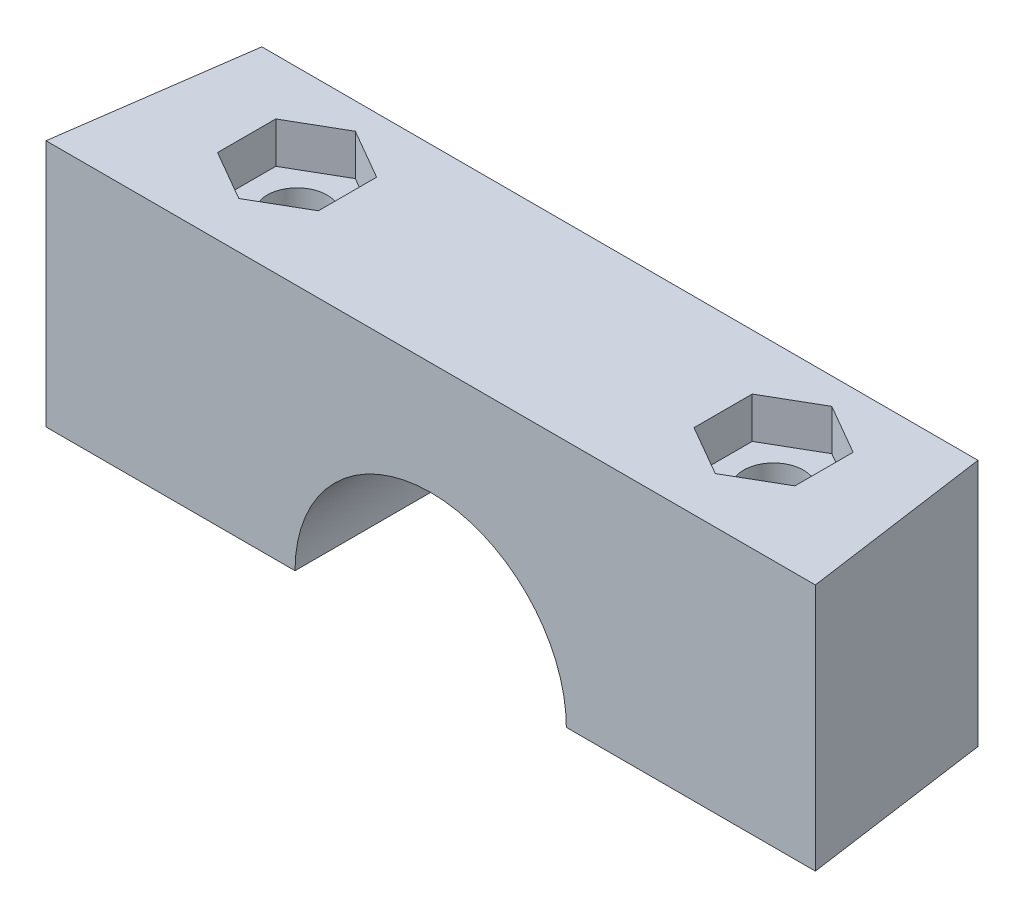
SolidWorks part; units mm, degrees
ref_plane "Front Plane" through (0, 0, 0) normal (0, 0, 1) x (1, 0, 0)
ref_plane "Top Plane" through (0, 0, 0) normal (0, 1, 0) x (1, 0, 0)
ref_plane "Right Plane" through (0, 0, 0) normal (1, 0, 0) x (0, 0, -1)
sketch "Sketch6" plane through (0, 0, 0) normal (0, 1, 0) x (1, 0, 0)
  line L0 (-16.8369, 5.7834) -> (13.1631, 5.7834)
  line L1 (13.1631, 5.7834) -> (20.6631, -47.5819)
  line L2 (20.6631, -47.5819) -> (-24.3369, -47.5819)
  line L3 (-24.3369, -47.5819) -> (-16.8369, 5.7834)
  circle A0 centre (13.1631, -5.2166) radius 1.78
  circle A1 centre (-16.8369, -5.2166) radius 1.78
  circle A2 centre (-26.4869, -43.0491) radius 1.78
  circle A3 centre (22.8131, -43.0491) radius 1.78
  dimension "D3" = 98
  dimension "D4" = 3.56
  dimension "D5" = 3.56
  dimension "D2" = 45
  dimension "D6" = 30
  dimension "D7" = 11
  dimension "D8" = 11
  dimension "D9" = 98
  dimension "D10" = 82
  dimension "D11" = 82
  dimension "D12" = 30
extrude "Boss-Extrude3" add sketch "Sketch6" along normal blind 14.5 contours L3 L0 L1 L2
sketch "Sketch8" plane through (0, 0, 47.5819) normal (0, 0, 1) x (1, 0, 0)
  line L0 (20.6631, 0) -> (-24.3369, 0) construction
  circle A0 centre (-1.8369, 0) radius 7.935
  dimension "D1" = 15.87
extrude "Cut-Extrude3" cut sketch "Sketch8" against normal blind 88
sketch "Sketch18" plane through (0, 14.5, 0) normal (0, 1, 0) x (1, 0, 0)
  line L0 (20.6631, -47.5819) -> (-24.3369, -47.5819) construction
  line L1 (-24.3369, -47.5819) -> (-16.8369, 5.7834) construction
  line L2 (13.1631, 5.7834) -> (20.6631, -47.5819) construction
  line L10 (-15.7718, -44.8683) -> (-12.8218, -43.1651)
  line L11 (-12.8218, -43.1651) -> (-12.8218, -39.7587)
  line L12 (-12.8218, -39.7587) -> (-15.7718, -38.0556)
  line L13 (-15.7718, -38.0556) -> (-18.7218, -39.7587)
  line L14 (-18.7218, -39.7587) -> (-18.7218, -43.1651)
  line L15 (-18.7218, -43.1651) -> (-15.7718, -44.8683)
  line L16 (12.098, -44.8683) -> (15.048, -43.1651)
  line L17 (15.048, -43.1651) -> (15.048, -39.7587)
  line L18 (15.048, -39.7587) -> (12.098, -38.0556)
  line L19 (12.098, -38.0556) -> (9.148, -39.7587)
  line L20 (9.148, -39.7587) -> (9.148, -43.1651)
  line L21 (9.148, -43.1651) -> (12.098, -44.8683)
  line L22 (11.3893, -26.016) -> (14.3893, -24.284)
  line L23 (14.3893, -24.284) -> (14.3893, -20.8199)
  line L24 (14.3893, -20.8199) -> (11.3893, -19.0878)
  line L25 (11.3893, -19.0878) -> (8.3893, -20.8199)
  line L26 (8.3893, -20.8199) -> (8.3893, -24.284)
  line L27 (8.3893, -24.284) -> (11.3893, -26.016)
  line L28 (-15.0632, -26.016) -> (-12.0632, -24.284)
  line L29 (-12.0632, -24.284) -> (-12.0632, -20.8199)
  line L30 (-12.0632, -20.8199) -> (-15.0632, -19.0878)
  line L31 (-15.0632, -19.0878) -> (-18.0632, -20.8199)
  line L32 (-18.0632, -20.8199) -> (-18.0632, -24.284)
  line L33 (-18.0632, -24.284) -> (-15.0632, -26.016)
  circle A0 centre (-15.0632, -22.5519) radius 3 construction
  circle A1 centre (-15.7718, -41.4619) radius 2.95 construction
  circle A2 centre (12.098, -41.4619) radius 2.95 construction
  circle A3 centre (11.3893, -22.5519) radius 3 construction
  point P0 (-15.7718, -41.4619)
  point P1 (-15.0632, -22.5519)
  point P2 (12.098, -41.4619)
  point P3 (11.3893, -22.5519)
  dimension "D1" = 6.12
  dimension "D2" = 7.63
  dimension "D3" = 25.03
  dimension "D4" = 5.7
  dimension "D5" = 6.12
  dimension "D6" = 7.63
  dimension "D7" = 25.03
  dimension "D8" = 5.7
  dimension "D9" = 6
  dimension "D10" = 5.9
  dimension "D11" = 5.9
  dimension "D12" = 6
sketch "Sketch19" plane through (0, 0, 0) normal (0, -1, 0) x (1, 0, 0)
  line L1 (-20.0152, 40.7177) -> (-17.249, 37.4149)
  line L2 (-17.249, 37.4149) -> (-13.0056, 38.1592)
  line L3 (-13.0056, 38.1592) -> (-11.5284, 42.2062)
  line L4 (-11.5284, 42.2062) -> (-14.2947, 45.5089)
  line L5 (-14.2947, 45.5089) -> (-18.5381, 44.7647)
  line L6 (-18.5381, 44.7647) -> (-20.0152, 40.7177)
  line L7 (-16.9187, 22.0232) -> (-15.5331, 20.6806)
  line L8 (-15.5331, 20.6806) -> (-13.6775, 21.2093)
  line L9 (-13.6775, 21.2093) -> (-13.2076, 23.0806)
  line L10 (-13.2076, 23.0806) -> (-14.5932, 24.4232)
  line L11 (-14.5932, 24.4232) -> (-16.4488, 23.8945)
  line L12 (-16.4488, 23.8945) -> (-16.9187, 22.0232)
  line L13 (16.8606, 20.993) -> (15.475, 26.5108)
  line L14 (15.475, 26.5108) -> (10.0037, 28.0696)
  line L15 (10.0037, 28.0696) -> (5.918, 24.1108)
  line L16 (5.918, 24.1108) -> (7.3037, 18.5931)
  line L17 (7.3037, 18.5931) -> (12.775, 17.0342)
  line L18 (12.775, 17.0342) -> (16.8606, 20.993)
  line L19 (20.0445, 40.0682) -> (17.2783, 47.6469)
  line L20 (17.2783, 47.6469) -> (9.3318, 49.0407)
  line L21 (9.3318, 49.0407) -> (4.1515, 42.8557)
  line L22 (4.1515, 42.8557) -> (6.9177, 35.2769)
  line L23 (6.9177, 35.2769) -> (14.8642, 33.8832)
  line L24 (14.8642, 33.8832) -> (20.0445, 40.0682)
  circle A0 centre (-15.7718, 41.4619) radius 3.731 construction
  circle A1 centre (-15.0632, 22.5519) radius 1.6709 construction
  circle A2 centre (11.3893, 22.5519) radius 4.9269 construction
  circle A3 centre (12.098, 41.4619) radius 6.9869 construction
  point P0 (-15.7718, 41.4619)
  point P1 (-15.0632, 22.5519)
  point P3 (11.3893, 22.5519)
  point P5 (12.098, 41.4619)
extrude "Cut-Extrude9" cut sketch "Sketch18" against normal blind 2.4
hole_wizard "#39 (0.13779528) Diameter Hole1" positions "3DSketch1" profile "Sketch21" hole size "#39" standard "ANSI Inch" end condition through all
sketch3d "3DSketch1"
  point P0 (-15.0632, 14.5, 22.5519)
  point P3 (11.3893, 14.5, 22.5519)
  point P6 (-15.7718, 14.5, 41.4619)
  point P9 (12.098, 14.5, 41.4619)
sketch "Sketch21" plane through (-15.0632, 14.5, 22.5519) normal (1, 0, 0) x (0, 0, 1)
  line L0 (0, 0) -> (0, 14.5)
  line L1 (0, 14.5) -> (1.75, 14.5)
  line L2 (1.75, 14.5) -> (1.75, 0)
  line L5 (1.75, 0) -> (0, 0)
  line L11 (0, -6.35) -> (0, 107.95) construction
  dimension "Thru Hole Dia." = 3.5
  dimension "Thru Hole Depth" = 14.5
sketch "Sketch22" plane through (0, 14.5, 0) normal (0, 1, 0) x (1, 0, 0)
  line L0 (-22.7813, -36.5132) -> (19.1075, -36.5132)
  line L1 (-24.3369, -47.5819) -> (-16.8369, 5.7834) construction
  line L2 (13.1631, 5.7834) -> (20.6631, -47.5819) construction
  line L3 (19.1075, -36.5132) -> (13.1631, 5.7834)
  line L4 (13.1631, 5.7834) -> (-16.8369, 5.7834)
  line L5 (-16.8369, 5.7834) -> (-22.7813, -36.5132)
extrude "Cut-Extrude10" cut sketch "Sketch22" against normal blind 22.4
sketch "Sketch24" plane through (0, 0, 0) normal (0, -1, 0) x (1, 0, 0)
  line L1 (-15.7718, 38.0556) -> (-12.8218, 39.7587)
  line L2 (-12.8218, 39.7587) -> (-12.8218, 43.1651)
  line L3 (-12.8218, 43.1651) -> (-15.7718, 44.8683)
  line L4 (-15.7718, 44.8683) -> (-18.7218, 43.1651)
  line L5 (-18.7218, 43.1651) -> (-18.7218, 39.7587)
  line L6 (-18.7218, 39.7587) -> (-15.7718, 38.0556)
  line L7 (12.098, 38.0556) -> (15.048, 39.7587)
  line L8 (15.048, 39.7587) -> (15.048, 43.1651)
  line L9 (15.048, 43.1651) -> (12.098, 44.8683)
  line L10 (12.098, 44.8683) -> (9.148, 43.1651)
  line L11 (9.148, 43.1651) -> (9.148, 39.7587)
  line L12 (9.148, 39.7587) -> (12.098, 38.0556)
  circle A0 centre (-15.7718, 41.4619) radius 2.95 construction
  circle A1 centre (12.098, 41.4619) radius 2.95 construction
  point P0 (-15.7718, 41.4619)
  point P1 (12.098, 41.4619)
  dimension "D1" = 5.9
  dimension "D2" = 5.9
extrude "Cut-Extrude11" cut sketch "Sketch24" against normal blind 2.4
